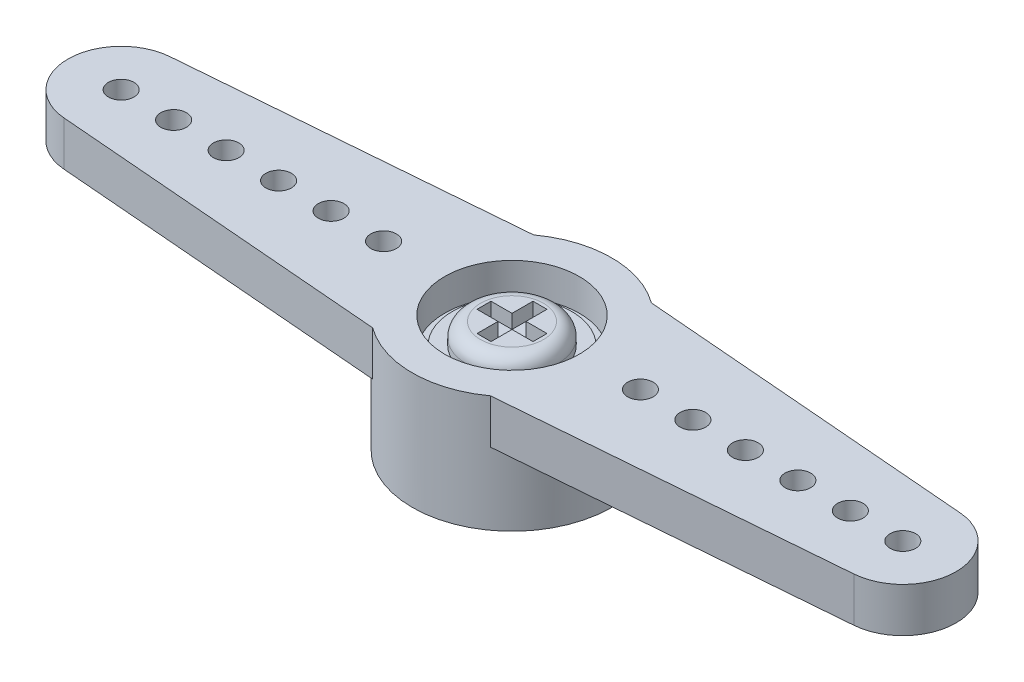
SolidWorks part; units mm, degrees
material "Nylon 101"
ref_plane "Front Plane" through (0, 0, 0) normal (0, 0, 1) x (1, 0, 0)
ref_plane "Top Plane" through (0, 0, 0) normal (0, 1, 0) x (1, 0, 0)
ref_plane "Right Plane" through (0, 0, 0) normal (1, 0, 0) x (0, 0, -1)
sketch "Sketch18" plane through (0, 0, 0) normal (0, 1, 0) x (1, 0, 0)
  line L0 (-16.1163, 0) -> (3.6195, 0) construction
  line L1 (-14.3431, 1.924) -> (-2.1374, 2.921)
  line L2 (-14.3431, -1.924) -> (-2.1374, -2.921)
  line L3 (0, 8.2238) -> (0, -7.484) construction
  line L4 (16.1163, 0) -> (-3.6195, 0) construction
  line L5 (14.3431, -1.924) -> (2.1374, -2.921)
  line L6 (14.3431, 1.924) -> (2.1374, 2.921)
  arc A0 (-2.1374, -2.921) -> (2.1374, -2.921) centre (0, 0) ccw
  arc A1 (-14.3431, 1.924) -> (-14.3431, -1.924) centre (-14.1859, 0) ccw
  arc A2 (14.3431, 1.924) -> (14.3431, -1.924) centre (14.1859, 0) cw
  arc A3 (2.1374, 2.921) -> (-2.1374, 2.921) centre (0, 0) ccw
  circle A4 centre (0, 0) radius 3.6195 construction
  dimension "D1" = 1.9304
  dimension "D2" = 3.6195
  dimension "D3" = 19.7358
  dimension "D4" = 5.842
extrude "Extrude17" add sketch "Sketch18" along normal blind 1.6129
sketch "Sketch19" plane through (0, 1.6129, 0) normal (0, 1, 0) x (1, 0, 0)
  circle A0 centre (0, 0) radius 3.6195
  arc A1 (-2.1374, -2.921) -> (2.1374, -2.921) centre (0, 0) ccw construction
extrude "Extrude19" add sketch "Sketch19" against normal blind 4.2291
sketch "Sketch20" plane through (0, 1.6129, 0) normal (0, 1, 0) x (1, 0, 0)
  line L0 (-14.1859, 0) -> (-12.2809, 0) construction
  line L1 (-12.2809, 0) -> (-10.3759, 0) construction
  line L2 (-10.3759, 0) -> (-8.4709, 0) construction
  line L3 (-8.4709, 0) -> (-6.5659, 0) construction
  line L4 (-6.5659, 0) -> (-4.6609, 0) construction
  line L5 (-4.6609, 0) -> (-2.7559, 0) construction
  line L6 (-2.7559, 0) -> (2.7559, 0) construction
  line L7 (0, 7.6883) -> (0, -8.0383) construction
  line L8 (4.6609, 0) -> (2.7559, 0) construction
  line L9 (6.5659, 0) -> (4.6609, 0) construction
  line L10 (8.4709, 0) -> (6.5659, 0) construction
  line L11 (10.3759, 0) -> (8.4709, 0) construction
  line L12 (12.2809, 0) -> (10.3759, 0) construction
  line L13 (14.1859, 0) -> (12.2809, 0) construction
  circle A0 centre (-14.1859, 0) radius 0.4636
  circle A1 centre (0, 0) radius 1.27
  circle A2 centre (12.2809, 0) radius 0.4636
  circle A3 centre (-4.6609, 0) radius 0.4636
  circle A4 centre (-6.5659, 0) radius 0.4636
  circle A5 centre (-8.4709, 0) radius 0.4636
  circle A6 centre (-10.3759, 0) radius 0.4636
  circle A7 centre (-12.2809, 0) radius 0.4636
  circle A8 centre (10.3759, 0) radius 0.4636
  circle A9 centre (8.4709, 0) radius 0.4636
  circle A10 centre (6.5659, 0) radius 0.4636
  circle A11 centre (4.6609, 0) radius 0.4636
  circle A12 centre (14.1859, 0) radius 0.4636
  dimension "D1" = 0.9271
  dimension "D3" = 2.54
  dimension "D2" = 1.905
extrude "Extrude20" cut sketch "Sketch20" against normal through all
sketch "Sketch21" plane through (0, 1.6129, 0) normal (0, 1, 0) x (1, 0, 0)
  circle A0 centre (0, 0) radius 2.4447
  dimension "D1" = 4.8895
extrude "Extrude21" cut sketch "Sketch21" against normal blind 1.1557
sketch "Sketch22" plane through (0, -2.6162, 0) normal (0, -1, 0) x (1, 0, 0)
  circle A0 centre (0, 0) radius 2.286
  dimension "D1" = 4.572
extrude "Extrude22" cut sketch "Sketch22" against normal blind 2.3368
sketch "Sketch23" plane through (0, 0.4572, 0) normal (0, 1, 0) x (1, 0, 0)
  circle A0 centre (0, 0) radius 2.159
  dimension "D1" = 4.318
extrude "Extrude23" add sketch "Sketch23" along normal blind 0.2032 separate body
sketch "Sketch24" plane through (0, 0.6604, 0) normal (0, 1, 0) x (1, 0, 0)
  circle A0 centre (0, 0) radius 1.651
  dimension "D1" = 3.302
extrude "Extrude24" add sketch "Sketch24" along normal blind 0.762
sketch "Sketch25" plane through (0, 1.4224, 0) normal (0, 1, 0) x (1, 0, 0)
  line L0 (0, -1.651) -> (0, 1.651) construction
  line L1 (-1.651, 0) -> (1.651, 0) construction
  line L2 (0.254, -1.016) -> (-0.254, -1.016)
  line L3 (-0.254, -1.016) -> (-0.254, -0.254)
  line L4 (-0.254, -0.254) -> (-1.016, -0.254)
  line L5 (-1.016, -0.254) -> (-1.016, 0.254)
  line L6 (0.254, 1.016) -> (-0.254, 1.016)
  line L7 (-0.254, 1.016) -> (-0.254, 0.254)
  line L8 (-0.254, 0.254) -> (-1.016, 0.254)
  line L9 (0.254, 1.016) -> (0.254, 0.254)
  line L10 (0.254, -1.016) -> (0.254, -0.254)
  line L11 (0.254, -0.254) -> (1.016, -0.254)
  line L12 (1.016, -0.254) -> (1.016, 0.254)
  line L13 (0.254, 0.254) -> (1.016, 0.254)
  circle A0 centre (0, 0) radius 1.651 construction
  point P16 (-1.016, 0)
  point P17 (0, 1.016)
  point P19 (0, -1.016)
  dimension "D1" = 2.032
  dimension "D2" = 0.508
extrude "Extrude25" cut sketch "Sketch25" against normal blind 0.508
fillet "Fillet1" radius 0.508 1 edges at (0, 1.4224, 1.651)
